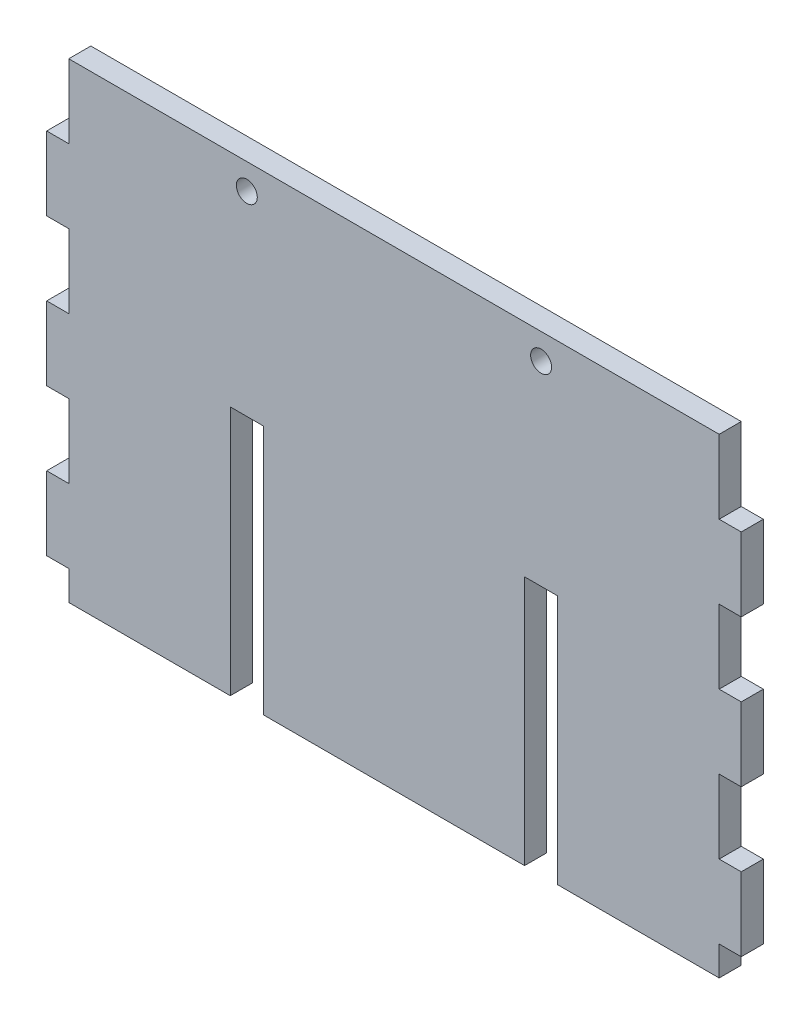
SolidWorks part; units mm, degrees
material "Acrylic (Medium-high impact)"
ref_plane "Front Plane" through (0, 0, 0) normal (0, 0, 1) x (1, 0, 0)
ref_plane "Top Plane" through (0, 0, 0) normal (0, 1, 0) x (1, 0, 0)
ref_plane "Right Plane" through (0, 0, 0) normal (1, 0, 0) x (0, 0, -1)
sketch "Sketch1" plane through (0, 0, 0) normal (0, 0, 1) x (1, 0, 0)
  line L1 (-47.2, -32) -> (47.2, -32)
  line L2 (-47.2, -32) -> (-47.2, 32)
  line L3 (-47.2, 32) -> (47.2, 32)
  line L4 (47.2, -32) -> (47.2, 32)
  line L5 (-47.2, -32) -> (47.2, 32) construction
  line L6 (-47.2, 32) -> (47.2, -32) construction
  point P0 (0, 0)
  dimension "D1" = 94.4
  dimension "D2" = 64
extrude "Boss-Extrude1" add sketch "Sketch1" along normal blind 3 contours L3 L4 L1 L2
sketch "Sketch2" plane through (0, 0, 0) normal (0, 0, -1) x (-1, 0, 0)
  line L0 (-44.2, 32) -> (-44.2, -32) construction
  line L1 (47.2, 32) -> (-47.2, 32) construction
  line L2 (47.2, -32) -> (-47.2, -32) construction
  line L3 (-47.2, -32) -> (-47.2, 32) construction
  line L4 (-47.2, 12) -> (-47.2, 2)
  line L5 (-47.2, 32) -> (-44.2, 32)
  line L6 (-47.2, 32) -> (-47.2, 22)
  line L7 (-47.2, 22) -> (-44.2, 22)
  line L8 (-44.2, 32) -> (-44.2, 22)
  line L9 (-47.2, 12) -> (-44.2, 12)
  line L10 (-44.2, 12) -> (-44.2, 2)
  line L11 (-47.2, 2) -> (-44.2, 2)
  line L12 (-47.2, -8) -> (-47.2, -18)
  line L13 (-47.2, -8) -> (-44.2, -8)
  line L14 (-44.2, -8) -> (-44.2, -18)
  line L15 (-47.2, -18) -> (-44.2, -18)
  line L16 (-47.2, -28) -> (-47.2, -38)
  line L17 (-47.2, -28) -> (-44.2, -28)
  line L18 (-44.2, -28) -> (-44.2, -38)
  line L19 (-47.2, -38) -> (-44.2, -38)
  line L20 (0, 0) -> (0, 32) construction
  line L21 (47.2, -38) -> (44.2, -38)
  line L22 (44.2, -28) -> (44.2, -38)
  line L23 (47.2, -28) -> (44.2, -28)
  line L24 (47.2, -28) -> (47.2, -38)
  line L25 (47.2, -18) -> (44.2, -18)
  line L26 (44.2, -8) -> (44.2, -18)
  line L27 (47.2, -8) -> (44.2, -8)
  line L28 (47.2, -8) -> (47.2, -18)
  line L29 (47.2, 2) -> (44.2, 2)
  line L30 (44.2, 12) -> (44.2, 2)
  line L31 (47.2, 12) -> (44.2, 12)
  line L32 (44.2, 32) -> (44.2, 22)
  line L33 (47.2, 22) -> (44.2, 22)
  line L34 (47.2, 32) -> (47.2, 22)
  line L35 (47.2, 32) -> (44.2, 32)
  line L36 (47.2, 12) -> (47.2, 2)
  point P26 (0, 0)
  dimension "D1" = 3
  dimension "D2" = 10
  dimension "D4" = 10
  dimension "D3" = 4
extrude "Cut-Extrude1" cut sketch "Sketch2" against normal blind 3
sketch "Sketch3" plane through (0, 0, 0) normal (0, 0, -1) x (-1, 0, 0)
  line L0 (0, 32) -> (0, -32) construction
  line L1 (-22.25, 2) -> (-17.75, 2)
  line L2 (-22.25, 2) -> (-22.25, -32)
  line L3 (-22.25, -32) -> (-17.75, -32)
  line L4 (-17.75, 2) -> (-17.75, -32)
  line L5 (-22.25, 2) -> (-17.75, -32) construction
  line L6 (-22.25, -32) -> (-17.75, 2) construction
  line L7 (44.2, 32) -> (-44.2, 32) construction
  line L8 (44.2, -32) -> (-44.2, -32) construction
  line L9 (22.25, -32) -> (17.75, -32)
  line L10 (22.25, 2) -> (22.25, -32)
  line L11 (22.25, 2) -> (17.75, 2)
  line L12 (17.75, 2) -> (17.75, -32)
  point P0 (-20, -15)
  dimension "D1" = 4.5
  dimension "D2" = 20
  dimension "D3" = 30
extrude "Cut-Extrude2" cut sketch "Sketch3" against normal blind 10
sketch "Sketch4" plane through (0, 0, 0) normal (0, 0, -1) x (-1, 0, 0)
  line L0 (-20, 2) -> (-20, 32) construction
  line L1 (-17.75, 2) -> (-22.25, 2) construction
  line L2 (44.2, 32) -> (-44.2, 32) construction
  line L3 (20, 2) -> (20, 32) construction
  line L4 (22.25, 2) -> (17.75, 2) construction
  circle A0 centre (-20, 28.5) radius 1.4224
  circle A1 centre (20, 28.5) radius 1.4224
  point P14 (0, 0)
  dimension "D1" = 2.8448
  dimension "D2" = 3.5
extrude "Cut-Extrude3" cut sketch "Sketch4" against normal blind 6
